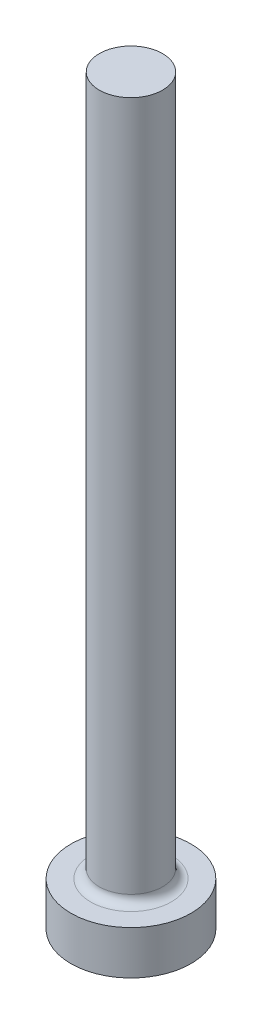
SolidWorks part; units mm, degrees
material "PLA-填充率10%"
ref_plane "前视基准面" through (0, 0, 0) normal (0, 0, 1) x (1, 0, 0)
ref_plane "上视基准面" through (0, 0, 0) normal (0, 1, 0) x (1, 0, 0)
ref_plane "右视基准面" through (0, 0, 0) normal (1, 0, 0) x (0, 0, -1)
sketch "草图1" plane through (0, 0, 0) normal (0, 1, 0) x (1, 0, 0)
  circle A0 centre (0, 0) radius 2.75
  dimension "D1" = 5.5
extrude "凸台-拉伸1" add sketch "草图1" along normal blind 2
sketch "草图2" plane through (0, 2, 0) normal (0, 1, 0) x (1, 0, 0)
  circle A0 centre (0, 0) radius 1.45
  dimension "D1" = 2.9
extrude "凸台-拉伸2" add sketch "草图2" along normal blind 32
fillet "圆角1" radius 0.4 1 edges at (0, 2, 1.45)
